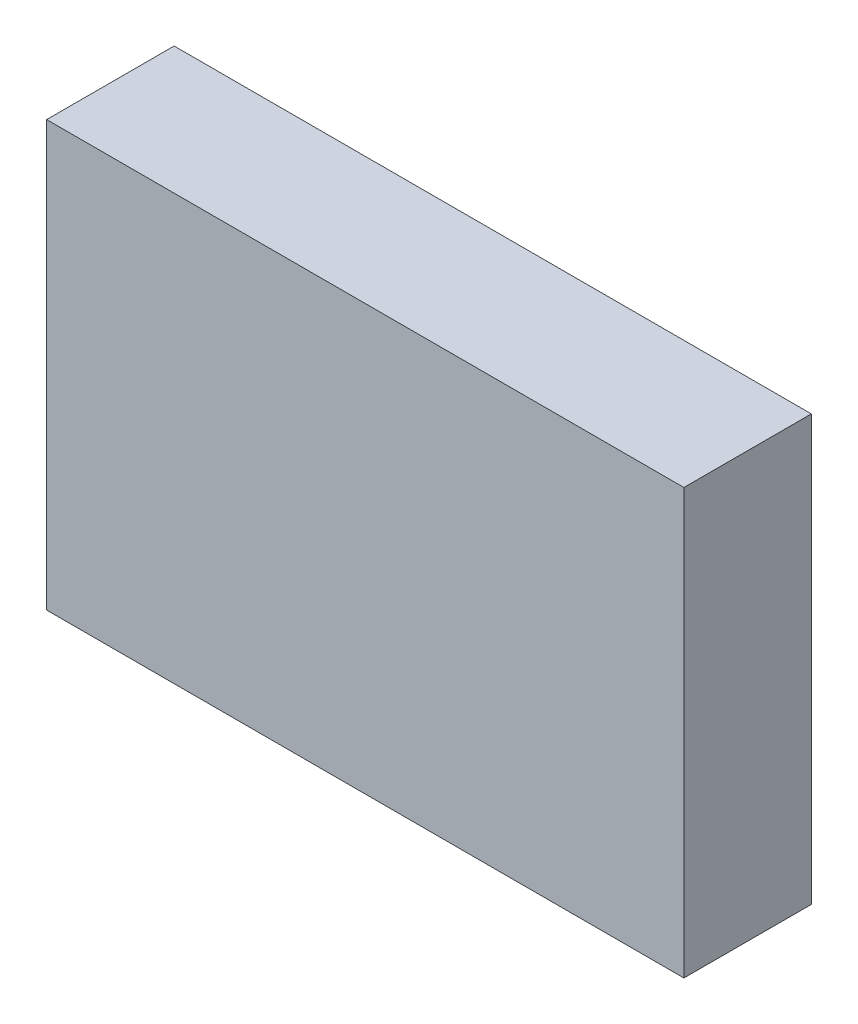
SolidWorks part; units mm, degrees
ref_plane "前视基准面" through (0, 0, 0) normal (0, 0, 1) x (1, 0, 0)
ref_plane "上视基准面" through (0, 0, 0) normal (0, 1, 0) x (1, 0, 0)
ref_plane "右视基准面" through (0, 0, 0) normal (1, 0, 0) x (0, 0, -1)
sketch "草图1" plane through (0, 0, 0) normal (0, 0, 1) x (1, 0, 0)
  line L1 (-30, 20) -> (30, 20)
  line L2 (-30, 20) -> (-30, -20)
  line L3 (-30, -20) -> (30, -20)
  line L4 (30, 20) -> (30, -20)
  line L5 (-30, 20) -> (30, -20) construction
  line L6 (-30, -20) -> (30, 20) construction
  point P0 (0, 0)
  dimension "D1" = 40
  dimension "D2" = 60
extrude "凸台-拉伸1" add sketch "草图1" along normal blind 12
sketch "草图2" plane through (0, 0, 0) normal (0, 0, -1) x (-1, 0, 0)
  circle A0 centre (0, 0) radius 10
extrude "切除-拉伸1" cut sketch "草图2" against normal blind 3
